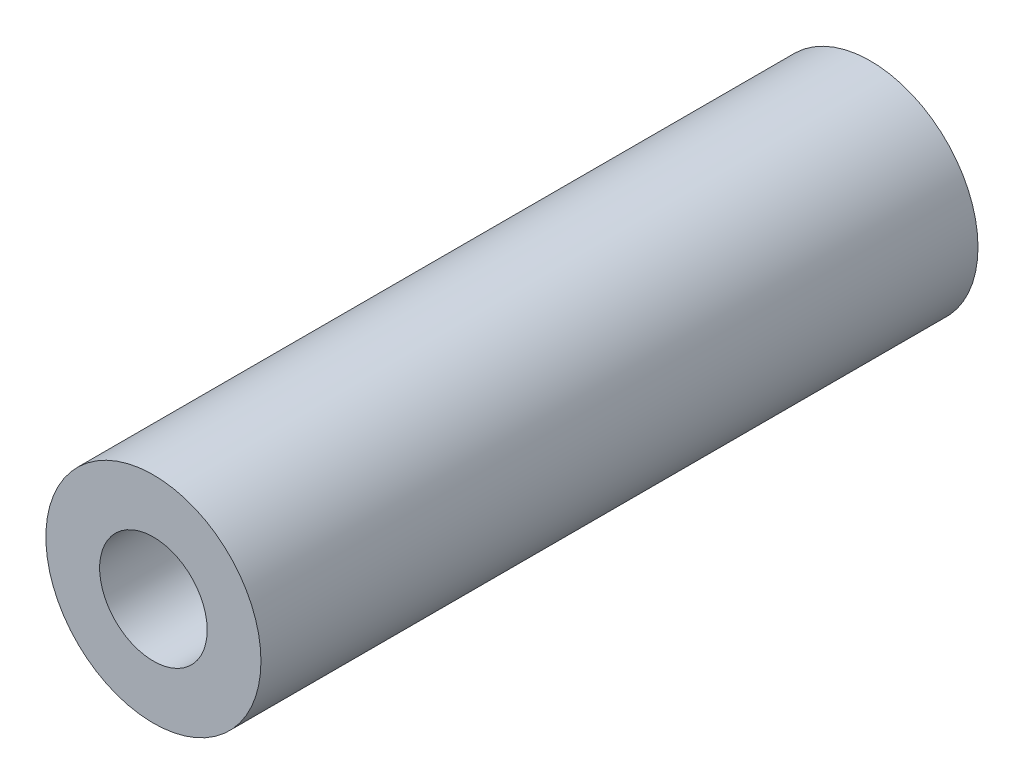
SolidWorks part; units mm, degrees
ref_plane "Front Plane" through (0, 0, 0) normal (0, 0, 1) x (1, 0, 0)
ref_plane "Top Plane" through (0, 0, 0) normal (0, 1, 0) x (1, 0, 0)
ref_plane "Right Plane" through (0, 0, 0) normal (1, 0, 0) x (0, 0, -1)
sketch "Esquisse1" plane through (0, 0, 0) normal (0, 0, 1) x (1, 0, 0)
  circle A0 centre (0, 0) radius 1.5
  circle A1 centre (0, 0) radius 3
  dimension "D1" = 6
  dimension "D2" = 3
extrude "Main" add sketch "Esquisse1" along normal blind 20
